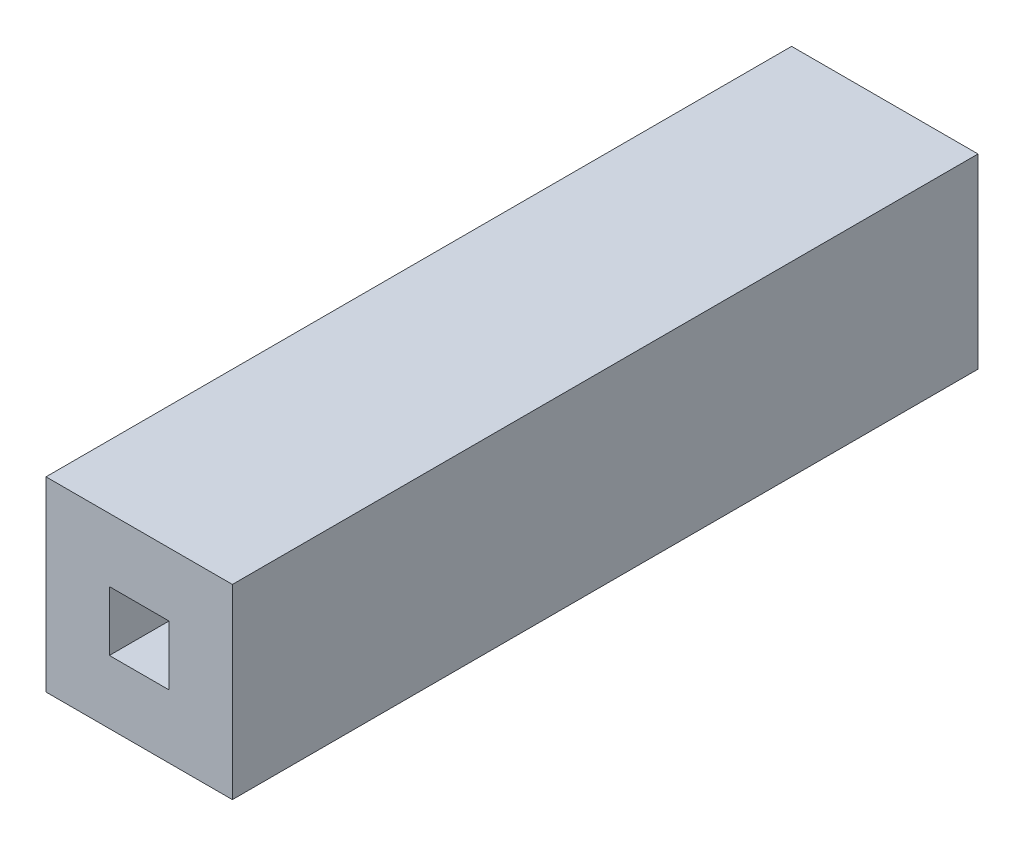
SolidWorks part; units mm, degrees
ref_plane "Front Plane" through (0, 0, 0) normal (0, 0, 1) x (1, 0, 0)
ref_plane "Top Plane" through (0, 0, 0) normal (0, 1, 0) x (1, 0, 0)
ref_plane "Right Plane" through (0, 0, 0) normal (1, 0, 0) x (0, 0, -1)
curve "Curve1"
  spline degree 3 poles (1, 0, 0) (0.9988, 0.0002, 0) (0.9943, 0.0009, 0) (0.9843, 0.0028, 0) (0.9682, 0.0061, 0) (0.9465, 0.0107, 0) (0.9197, 0.0165, 0) (0.8883, 0.0232, 0) (0.8526, 0.0307, 0) (0.8133, 0.0391, 0) (0.7709, 0.048, 0) (0.726, 0.0572, 0) (0.6794, 0.0664, 0) (0.6313, 0.0753, 0) (0.5825, 0.0836, 0) (0.5333, 0.091, 0) (0.4843, 0.0974, 0) (0.4358, 0.1025, 0) (0.3883, 0.1061, 0) (0.3422, 0.1083, 0) (0.2979, 0.1088, 0) (0.2557, 0.1076, 0) (0.216, 0.1047, 0) (0.1791, 0.1001, 0) (0.1452, 0.094, 0) (0.1145, 0.0863, 0) (0.0871, 0.0772, 0) (0.0634, 0.067, 0) (0.0433, 0.0558, 0) (0.0269, 0.0439, 0) (0.0143, 0.0318, 0) (0.0056, 0.0197, 0) (0.001, 0.0089, 0) (0.0003, 0.0024, 0) (0, 0, 0) knots 0 0 0 0 0.003366 0.013244 0.029119 0.050454 0.076732 0.107578 0.142572 0.181154 0.222716 0.266609 0.312234 0.359018 0.406463 0.454076 0.501434 0.5481 0.593683 0.637833 0.680213 0.720555 0.758606 0.794166 0.827102 0.857328 0.884778 0.909434 0.931316 0.950526 0.967126 0.981232 0.993142 1 1 1 1
sketch "Sketch2" plane through (0, 0, 0) normal (0, 0, 1) x (1, 0, 0)
  line L1 (6.35, -6.35) -> (-6.35, -6.35)
  line L2 (6.35, -6.35) -> (6.35, 6.35)
  line L3 (6.35, 6.35) -> (-6.35, 6.35)
  line L4 (-6.35, -6.35) -> (-6.35, 6.35)
  line L5 (6.35, -6.35) -> (-6.35, 6.35) construction
  line L6 (6.35, 6.35) -> (-6.35, -6.35) construction
  point P0 (0, 0)
  dimension "D1" = 12.7
  dimension "D2" = 12.7
extrude "Boss-Extrude1" add sketch "Sketch2" along normal blind 50.8
sketch "Sketch4" plane through (0, 0, 0) normal (0, 0, -1) x (-1, 0, 0)
  line L1 (2.032, -2.032) -> (-2.032, -2.032)
  line L2 (2.032, -2.032) -> (2.032, 2.032)
  line L3 (2.032, 2.032) -> (-2.032, 2.032)
  line L4 (-2.032, -2.032) -> (-2.032, 2.032)
  line L5 (2.032, -2.032) -> (-2.032, 2.032) construction
  line L6 (2.032, 2.032) -> (-2.032, -2.032) construction
  point P0 (0, 0)
  dimension "D1" = 4.064
  dimension "D2" = 4.064
extrude "Cut-Extrude1" cut sketch "Sketch4" against normal through all
